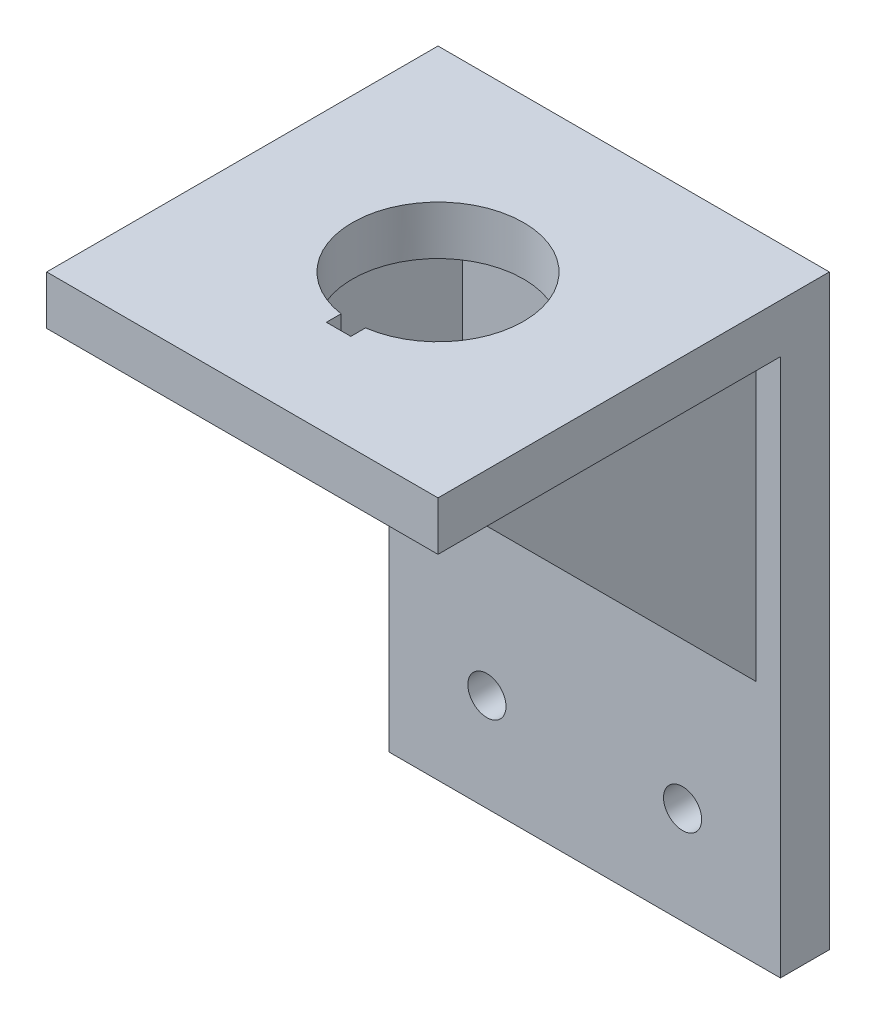
SolidWorks part; units mm, degrees
ref_plane "Front Plane" through (0, 0, 0) normal (0, 0, 1) x (1, 0, 0)
ref_plane "Top Plane" through (0, 0, 0) normal (0, 1, 0) x (1, 0, 0)
ref_plane "Right Plane" through (0, 0, 0) normal (1, 0, 0) x (0, 0, -1)
sketch "Sketch1" plane through (0, 0, 0) normal (0, 0, 1) x (1, 0, 0)
  line L1 (-25.4, -38.1) -> (25.4, -38.1)
  line L2 (-25.4, -38.1) -> (-25.4, 38.1)
  line L3 (-25.4, 38.1) -> (25.4, 38.1)
  line L4 (25.4, -38.1) -> (25.4, 38.1)
  line L5 (-25.4, -38.1) -> (25.4, 38.1) construction
  line L6 (-25.4, 38.1) -> (25.4, -38.1) construction
  circle A0 centre (-12.7, -25.4) radius 2.4765
  circle A1 centre (12.7, -25.4) radius 2.4765
  circle A2 centre (0, 25.4) radius 2.4765
  point P0 (0, 0)
  dimension "D3" = 4.953
  dimension "D1" = 50.8
  dimension "D2" = 76.2
  dimension "D4" = 12.7
  dimension "D5" = 12.7
  dimension "D6" = 12.7
  dimension "D7" = 12.7
extrude "Boss-Extrude1" add sketch "Sketch1" along normal blind 6.35
sketch "Sketch2" plane through (0, 0, 0) normal (0, 0, -1) x (-1, 0, 0)
  line L0 (-25.4, -38.1) -> (-25.4, 38.1) construction
  line L1 (25.4, 38.1) -> (25.4, -38.1) construction
  line L2 (-25.4, 38.1) -> (25.4, 38.1) construction
  arc A0 (-5.08, 13.3403) -> (-9.013, 11.0696) centre (0, 0) ccw
  arc A1 (-14.0704, 10.3423) -> (-15.9919, 7.0141) centre (0, 0) ccw
  arc A2 (5.08, 13.3403) -> (3.6169, 15.463) centre (5.8883, 15.463) cw
  arc A3 (3.6169, 15.463) -> (1.9215, 17.3565) centre (1.7119, 15.463) ccw
  arc A4 (-5.08, 13.3403) -> (-3.6169, 15.463) centre (-5.8883, 15.463) ccw
  arc A5 (-1.9215, 17.3565) -> (-3.6169, 15.463) centre (-1.7119, 15.463) ccw
  arc A6 (14.0704, 10.3423) -> (11.5829, 10.8638) centre (12.5354, 9.2141) ccw
  arc A7 (9.013, 11.0696) -> (11.5829, 10.8638) centre (10.4472, 12.831) ccw
  arc A8 (15.1998, 4.5992) -> (15.9919, 7.0141) centre (14.2473, 6.249) ccw
  arc A9 (14.093, 2.2707) -> (15.1998, 4.5992) centre (16.3355, 2.6321) cw
  arc A10 (15.9919, -7.0141) -> (15.1998, -4.5992) centre (14.2473, -6.249) ccw
  arc A11 (14.093, -2.2707) -> (15.1998, -4.5992) centre (16.3355, -2.6321) ccw
  arc A12 (11.5829, -10.8638) -> (14.0704, -10.3423) centre (12.5354, -9.2141) ccw
  arc A13 (9.013, -11.0696) -> (11.5829, -10.8638) centre (10.4472, -12.831) cw
  arc A14 (1.9215, -17.3565) -> (3.6169, -15.463) centre (1.7119, -15.463) ccw
  arc A15 (5.08, -13.3403) -> (3.6169, -15.463) centre (5.8883, -15.463) ccw
  arc A16 (-3.6169, -15.463) -> (-1.9215, -17.3565) centre (-1.7119, -15.463) ccw
  arc A17 (-5.08, -13.3403) -> (-3.6169, -15.463) centre (-5.8883, -15.463) cw
  arc A18 (-14.0704, -10.3423) -> (-11.5829, -10.8638) centre (-12.5354, -9.2141) ccw
  arc A19 (-9.013, -11.0696) -> (-11.5829, -10.8638) centre (-10.4472, -12.831) ccw
  arc A20 (-15.1998, -4.5992) -> (-15.9919, -7.0141) centre (-14.2473, -6.249) ccw
  arc A21 (-14.093, -2.2707) -> (-15.1998, -4.5992) centre (-16.3355, -2.6321) cw
  arc A22 (-15.9919, 7.0141) -> (-15.1998, 4.5992) centre (-14.2473, 6.249) ccw
  arc A23 (-14.093, 2.2707) -> (-15.1998, 4.5992) centre (-16.3355, 2.6321) ccw
  arc A24 (-11.5829, 10.8638) -> (-14.0704, 10.3423) centre (-12.5354, 9.2141) ccw
  arc A25 (-9.013, 11.0696) -> (-11.5829, 10.8638) centre (-10.4472, 12.831) cw
  arc A26 (1.9215, 17.3565) -> (-1.9215, 17.3565) centre (0, 0) ccw
  arc A27 (15.9919, 7.0141) -> (14.0704, 10.3423) centre (0, 0) ccw
  arc A28 (14.0704, -10.3423) -> (15.9919, -7.0141) centre (0, 0) ccw
  arc A29 (-1.9215, -17.3565) -> (1.9215, -17.3565) centre (0, 0) ccw
  arc A30 (-15.9919, -7.0141) -> (-14.0704, -10.3423) centre (0, 0) ccw
  arc A31 (-14.093, 2.2707) -> (-14.093, -2.2707) centre (0, 0) ccw
  arc A32 (-9.013, -11.0696) -> (-5.08, -13.3403) centre (0, 0) ccw
  arc A33 (5.08, -13.3403) -> (9.013, -11.0696) centre (0, 0) ccw
  arc A34 (14.093, -2.2707) -> (14.093, 2.2707) centre (0, 0) ccw
  arc A35 (9.013, 11.0696) -> (5.08, 13.3403) centre (0, 0) ccw
  circle A36 centre (-12.7, 25.4) radius 2.2225
  circle A37 centre (12.7, 25.4) radius 2.2225
  point P67 (0, 0)
  dimension "D1" = 28.5496
  dimension "D2" = 34.925
  dimension "D4" = 1.905
  dimension "D9" = 4.445
  dimension "D3" = 10.16
  dimension "D6" = 12.7
  dimension "D7" = 12.7
  dimension "D8" = 12.7
  dimension "D5" = 6
extrude "Boss-Extrude2" add sketch "Sketch2" along normal blind 3.175
sketch "Sketch3" plane through (0, 0, -3.175) normal (0, 0, -1) x (-1, 0, 0)
  line L1 (-3.175, -1.5875) -> (3.175, -1.5875)
  line L2 (-3.175, -1.5875) -> (-3.175, 1.5875)
  line L3 (-3.175, 1.5875) -> (3.175, 1.5875)
  line L4 (3.175, -1.5875) -> (3.175, 1.5875)
  line L5 (-3.175, -1.5875) -> (3.175, 1.5875) construction
  line L6 (-3.175, 1.5875) -> (3.175, -1.5875) construction
  point P0 (0, 0)
  dimension "D1" = 6.35
  dimension "D2" = 3.175
extrude "Cut-Extrude1" cut sketch "Sketch3" against normal through all
sketch "Sketch4" plane through (0, 38.1, 0) normal (0, 1, 0) x (1, 0, 0)
  line L0 (25.4, 0) -> (-25.4, 0) construction
  line L1 (-25.4, -6.35) -> (25.4, -6.35)
  line L2 (-25.4, -6.35) -> (-25.4, -50.8)
  line L3 (-25.4, -50.8) -> (25.4, -50.8)
  line L4 (25.4, -6.35) -> (25.4, -50.8)
  dimension "D1" = 50.8
extrude "Boss-Extrude3" add sketch "Sketch4" against normal blind 6.35
sketch "Sketch5" plane through (0, 0, 0) normal (1, 0, 0) x (0, 0, -1)
  line L0 (-44.45, 31.75) -> (-6.35, -6.35)
  line L1 (-50.8, 31.75) -> (-6.35, 31.75) construction
  line L2 (-6.35, -38.1) -> (-6.35, 31.75) construction
  line L3 (-6.35, -6.35) -> (-6.35, 31.75)
  line L4 (-44.45, 31.75) -> (-6.35, 31.75)
  dimension "D1" = 38.1
extrude "Boss-Extrude4" add sketch "Sketch5" along normal mid plane 44.45
sketch "Sketch6" plane through (0, 0, 6.35) normal (0, 0, 1) x (1, 0, 0)
  line L0 (22.225, -6.35) -> (-22.225, -6.35) construction
  line L1 (-15.875, -6.35) -> (15.875, -6.35)
  line L2 (-15.875, -6.35) -> (-15.875, 31.75)
  line L3 (-15.875, 31.75) -> (15.875, 31.75)
  line L4 (15.875, -6.35) -> (15.875, 31.75)
  line L5 (22.225, 31.75) -> (-22.225, 31.75) construction
  line L7 (-22.225, 31.75) -> (-22.225, -6.35) construction
  point P8 (0, -6.35)
  dimension "D1" = 6.35
extrude "Cut-Extrude2" cut sketch "Sketch6" along normal through all
sketch "Sketch7" plane through (0, 31.75, 0) normal (0, -1, 0) x (1, 0, 0)
  line L0 (-25.4, 50.8) -> (25.4, 50.8) construction
  circle A0 centre (0, 25.4) radius 11.1125
  dimension "D2" = 22.225
  dimension "D1" = 25.4
extrude "Cut-Extrude3" cut sketch "Sketch7" against normal through all
sketch "Sketch8" plane through (0, 38.1, 0) normal (0, 1, 0) x (1, 0, 0)
  line L1 (-1.5875, -36.3985) -> (1.5875, -36.3985)
  line L2 (-1.5875, -36.3985) -> (-1.5875, -38.3035)
  line L3 (-1.5875, -38.3035) -> (1.5875, -38.3035)
  line L4 (1.5875, -36.3985) -> (1.5875, -38.3035)
  circle A0 centre (0, -25.4) radius 11.1125 construction
  point P6 (0, 0)
  dimension "D1" = 1.905
  dimension "D2" = 3.175
extrude "Cut-Extrude4" cut sketch "Sketch8" against normal blind 2.2225
